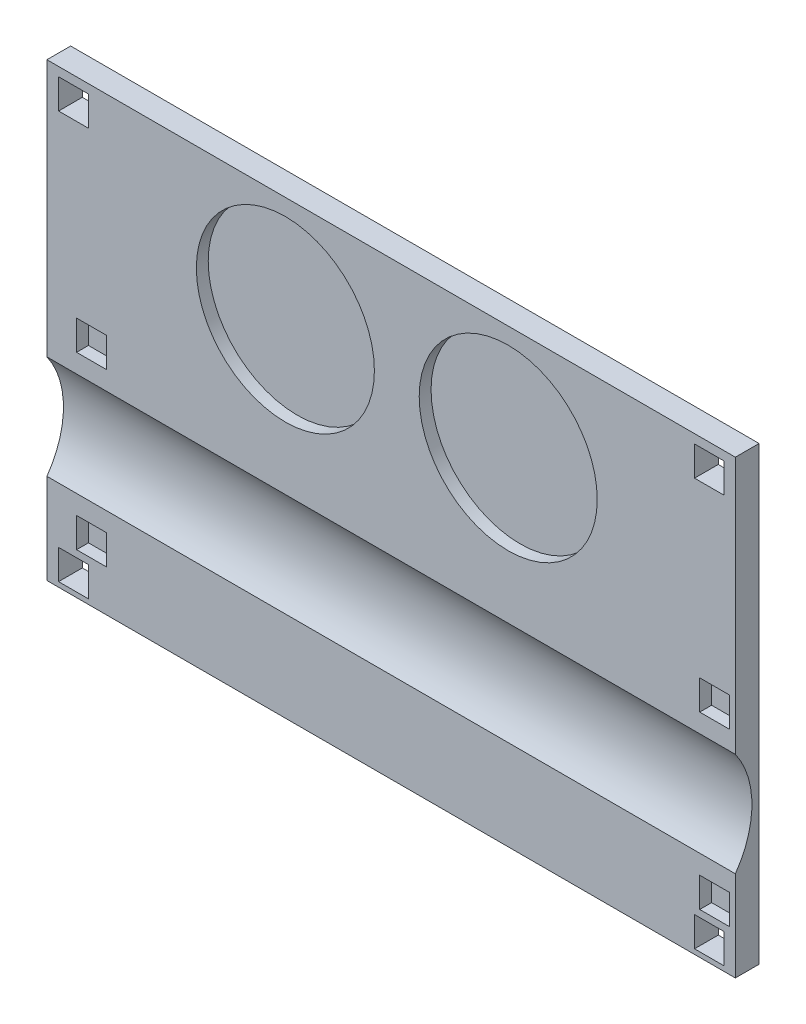
SolidWorks part; units mm, degrees
material "Beech"
ref_plane "Front Plane" through (0, 0, 0) normal (0, 0, 1) x (1, 0, 0)
ref_plane "Top Plane" through (0, 0, 0) normal (0, 1, 0) x (1, 0, 0)
ref_plane "Right Plane" through (0, 0, 0) normal (1, 0, 0) x (0, 0, -1)
sketch "Sketch3" plane through (0, 0, 0) normal (0, 0, 1) x (1, 0, 0)
  line L1 (12.0039, 40.6626) -> (159.3239, 40.6626)
  line L2 (12.0039, 40.6626) -> (12.0039, -55.8574)
  line L3 (12.0039, -55.8574) -> (159.3239, -55.8574)
  line L4 (159.3239, 40.6626) -> (159.3239, -55.8574)
extrude "Boss-Extrude1" add sketch "Sketch3" along normal blind 5.08
sketch "Sketch4" plane through (0, 0, 5.08) normal (0, 0, 1) x (1, 0, 0)
  line L18 (18.3539, -40.6174) -> (24.7039, -40.6174)
  line L19 (18.3539, -40.6174) -> (18.3539, -46.9674)
  line L20 (18.3539, -46.9674) -> (24.7039, -46.9674)
  line L21 (24.7039, -40.6174) -> (24.7039, -46.9674)
  line L22 (158.0539, -40.6174) -> (151.7039, -40.6174)
  line L23 (158.0539, -40.6174) -> (158.0539, -46.9674)
  line L24 (158.0539, -46.9674) -> (151.7039, -46.9674)
  line L25 (151.7039, -40.6174) -> (151.7039, -46.9674)
  line L26 (151.7039, -10.3914) -> (158.0539, -10.3914)
  line L27 (24.7039, -10.3914) -> (18.3539, -10.3914)
  line L28 (24.7039, -10.3914) -> (24.7039, -4.0414)
  line L29 (24.7039, -4.0414) -> (18.3539, -4.0414)
  line L30 (18.3539, -10.3914) -> (18.3539, -4.0414)
  line L31 (151.7039, -10.3914) -> (151.7039, -4.0414)
  line L32 (151.7039, -4.0414) -> (158.0539, -4.0414)
  line L33 (158.0539, -10.3914) -> (158.0539, -4.0414)
  circle A0 centre (63.0325, 18.0704) radius 19.05
  circle A1 centre (110.7187, 18.0704) radius 19.05
extrude "Cut-Extrude1" cut sketch "Sketch4" against normal blind 2.54
sketch "Sketch6" plane through (0, 0, 0) normal (0, 0, 1) x (1, 0, 0)
  line L1 (14.505, -48.4633) -> (20.855, -48.4633)
  line L2 (14.505, -48.4633) -> (14.505, -54.8133)
  line L3 (14.505, -54.8133) -> (20.855, -54.8133)
  line L4 (20.855, -48.4633) -> (20.855, -54.8133)
  line L5 (14.505, 38.7548) -> (20.855, 38.7548)
  line L6 (14.505, 38.7548) -> (14.505, 32.4048)
  line L7 (14.505, 32.4048) -> (20.855, 32.4048)
  line L8 (20.855, 38.7548) -> (20.855, 32.4048)
  line L9 (156.9417, 38.7548) -> (150.5917, 38.7548)
  line L10 (156.9417, 38.7548) -> (156.9417, 32.4048)
  line L11 (156.9417, 32.4048) -> (150.5917, 32.4048)
  line L12 (150.5917, 38.7548) -> (150.5917, 32.4048)
  line L13 (156.9417, -54.8133) -> (150.5917, -54.8133)
  line L14 (156.9417, -54.8133) -> (156.9417, -48.4633)
  line L15 (156.9417, -48.4633) -> (150.5917, -48.4633)
  line L16 (150.5917, -54.8133) -> (150.5917, -48.4633)
extrude "Cut-Extrude3" cut sketch "Sketch6" along normal blind 7.62
sketch "Sketch8" plane through (0, 0, 0) normal (0, 0, 1) x (1, 0, 0)
  line L3 (21.5289, -25.5044) -> (12.0039, -25.5044)
  line L4 (12.0039, 40.6626) -> (12.0039, -55.8574) construction
sketch "Sketch7" plane through (0, 0, 0) normal (1, 0, 0) x (0, 0, -1)
  circle A0 centre (-20.587, -25.4746) radius 19.05
extrude "Cut-Extrude4" cut sketch "Sketch7" along normal blind 171.45
